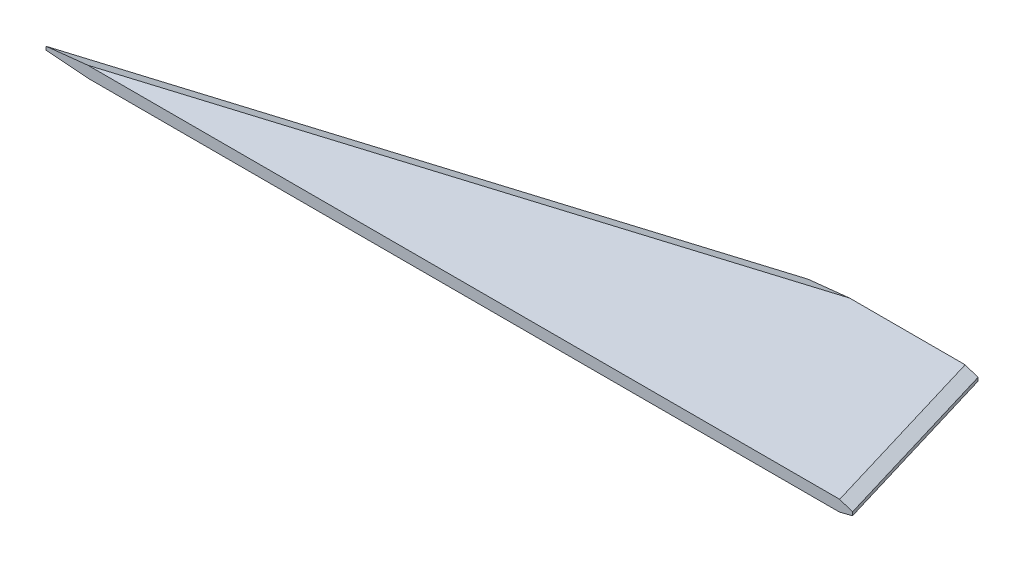
SolidWorks part; units mm, degrees
material "Thornel Mat VMA"
ref_plane "Front Plane" through (0, 0, 0) normal (0, 0, 1) x (1, 0, 0)
ref_plane "Top Plane" through (0, 0, 0) normal (0, 1, 0) x (1, 0, 0)
ref_plane "Right Plane" through (0, 0, 0) normal (1, 0, 0) x (0, 0, -1)
sketch "Sketch1" plane through (0, 0, 0) normal (0, 1, 0) x (1, 0, 0)
  line L0 (0, 0) -> (228.6, 0)
  line L1 (165.1, 50.8) -> (213.36, 50.8)
  line L2 (0, 0) -> (165.1, 50.8)
  line L3 (213.36, 50.8) -> (228.6, 0)
  dimension "D1" = 48.26
  dimension "D2" = 228.6
  dimension "D3" = 165.1
  dimension "D4" = 50.8
extrude "Boss-Extrude1" add sketch "Sketch1" along normal blind 3.175
chamfer "Chamfer1" distance 1.27 angle 70 2 edges at (82.55, 3.175, -25.4) (220.98, 3.175, -25.4)
chamfer "Chamfer2" distance 3.556 angle 15 2 edges at (220.98, 0, -25.4) (82.55, 0, -25.4)
